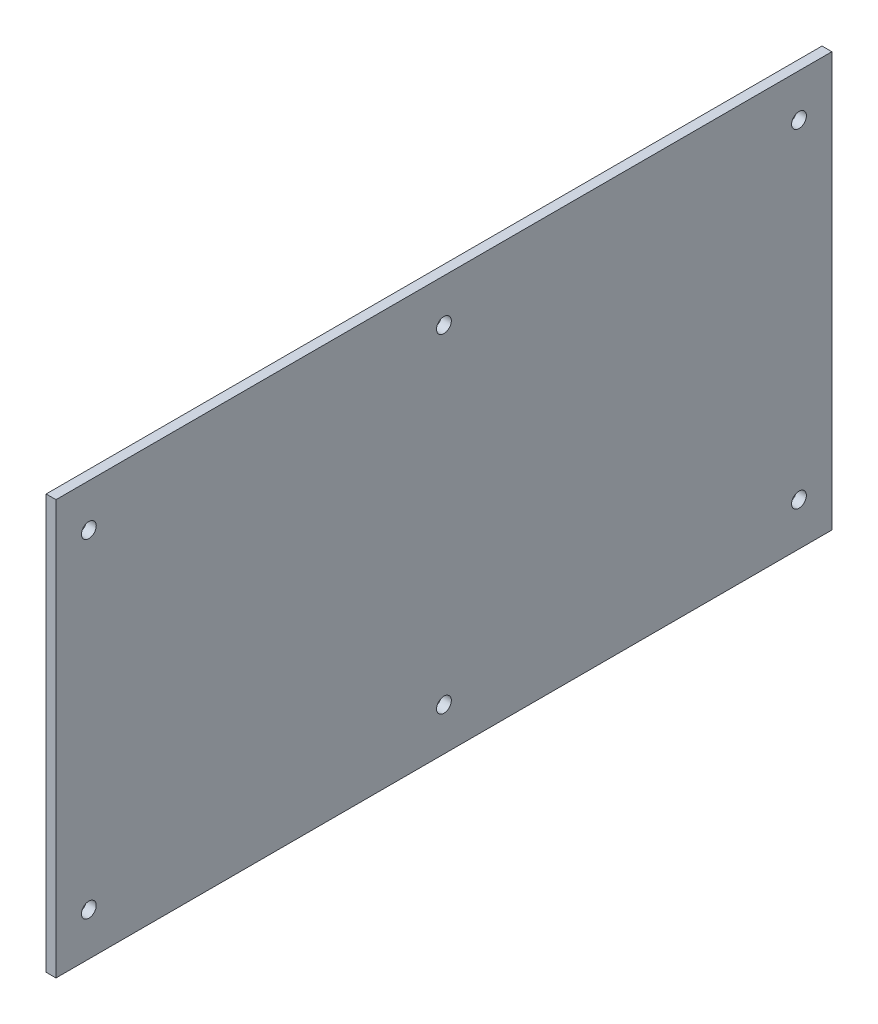
SolidWorks part; units mm, degrees
ref_plane "Спереди" through (0, 0, 0) normal (0, 0, 1) x (1, 0, 0)
ref_plane "Сверху" through (0, 0, 0) normal (0, 1, 0) x (1, 0, 0)
ref_plane "Справа" through (0, 0, 0) normal (1, 0, 0) x (0, 0, -1)
sketch "Эскиз1" plane through (20, 0, 0) normal (1, 0, 0) x (0, 0, -1)
  line L4 (0, -3) -> (0, 123)
  line L5 (0, 123) -> (-236, 123)
  line L6 (-236, 123) -> (-236, -3)
  line L7 (-236, -3) -> (0, -3)
  line L8 (0, -3) -> (0, 123)
  line L9 (0, 123) -> (-236, 123)
  line L10 (-236, 123) -> (-236, -3)
  line L11 (-236, -3) -> (0, -3)
  dimension "D1" = 0
extrude "Бобышка-Вытянуть1" add sketch "Эскиз1" along normal blind 3
sketch "Эскиз3" plane through (23, 0, 0) normal (1, 0, 0) x (0, 0, -1)
  line L0 (-10, 110) -> (-10, 10) construction
  line L1 (-10, 110) -> (-226, 110) construction
  line L2 (-10, 10) -> (-226, 10) construction
  line L3 (-226, 110) -> (-226, 10) construction
  line L4 (0, 123) -> (-236, 123) construction
  line L5 (-236, -3) -> (0, -3) construction
  line L6 (-236, 123) -> (-236, -3) construction
  line L7 (0, -3) -> (0, 123) construction
  circle A0 centre (-10, 110) radius 2.25
  circle A1 centre (-10, 10) radius 2.25
  circle A2 centre (-226, 110) radius 2.25
  circle A3 centre (-226, 10) radius 2.25
  circle A4 centre (-118, 110) radius 2.25
  circle A5 centre (-118, 10) radius 2.25
  dimension "D5" = 4.5
  dimension "D6" = 4.5
  dimension "D7" = 4.5
  dimension "D8" = 4.5
  dimension "D9" = 4.5
  dimension "D10" = 4.5
  dimension "D1" = 13
  dimension "D2" = 13
  dimension "D3" = 10
  dimension "D4" = 10
extrude "Вырез-Вытянуть1" cut sketch "Эскиз3" against normal through all
